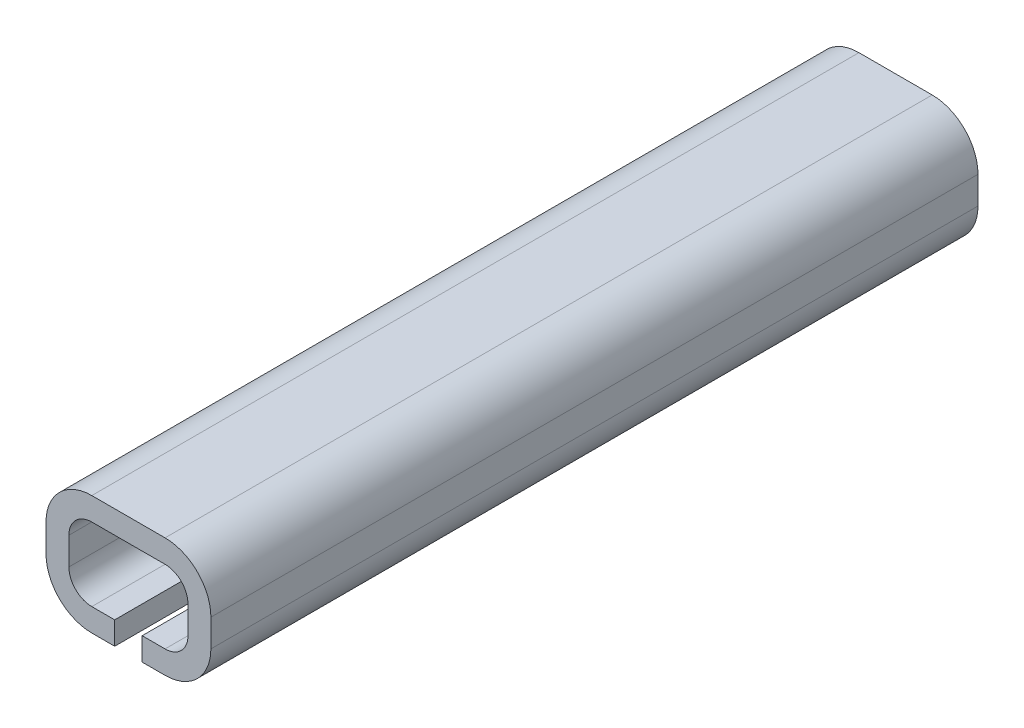
SolidWorks part; units mm, degrees
ref_plane "Plan de face" through (0, 0, 0) normal (0, 0, 1) x (1, 0, 0)
ref_plane "Plan de dessus" through (0, 0, 0) normal (0, 1, 0) x (1, 0, 0)
ref_plane "Plan de droite" through (0, 0, 0) normal (1, 0, 0) x (0, 0, -1)
sketch "Esquisse1" plane through (0, 0, 0) normal (0, 0, 1) x (1, 0, 0)
  line L1 (2.6, 0.6) -> (2.6, -0.6)
  line L2 (1.6, -1.6) -> (-1.6, -1.6)
  line L3 (-2.6, -0.6) -> (-2.6, 0.6)
  line L5 (3.6, 0.6) -> (3.6, -0.6)
  line L6 (1.6, -2.6) -> (-1.6, -2.6)
  line L7 (-3.6, -0.6) -> (-3.6, 0.6)
  line L16 (-1.6, 2.6) -> (1.6, 2.6) construction
  line L17 (1.6, 2.6) -> (0.1679, 2.6)
  line L18 (-1.6, 2.6) -> (0.1679, 2.6)
  line L19 (-1.6, 1.6) -> (1.6, 1.6)
  line L20 (-1.6, 1.6) -> (1.6, 1.6) construction
  arc A0 (-1.6, -1.6) -> (-2.6, -0.6) centre (-1.6, -0.6) cw
  arc A1 (2.6, -0.6) -> (1.6, -1.6) centre (1.6, -0.6) cw
  arc A2 (1.6, 1.6) -> (2.6, 0.6) centre (1.6, 0.6) cw
  arc A3 (-1.6, 1.6) -> (-2.6, 0.6) centre (-1.6, 0.6) ccw
  arc A4 (1.6, 2.6) -> (3.6, 0.6) centre (1.6, 0.6) cw
  arc A5 (3.6, -0.6) -> (1.6, -2.6) centre (1.6, -0.6) cw
  arc A6 (-1.6, -2.6) -> (-3.6, -0.6) centre (-1.6, -0.6) cw
  arc A7 (-1.6, 2.6) -> (-3.6, 0.6) centre (-1.6, 0.6) ccw
  point P6 (-2.6, -1.6)
  point P11 (5.1, 1.6)
  point P14 (-2.6, 1.6)
  point P15 (0, 1.6)
  point P16 (-2.6, 0)
  dimension "D3" = 1
  dimension "D1" = 3.2
  dimension "D2" = 5.2
  dimension "D9" = 3.2
  dimension "D4" = 1
extrude "Boss.-Extru.2" add sketch "Esquisse1" along normal blind 10
sketch "Esquisse7" plane through (0, 0, 0) normal (0, 0, -1) x (-1, 0, 0)
  line L8 (-3.6, 0.6) -> (-3.6, -0.6)
  line L9 (-1.6, -2.6) -> (1.6, -2.6)
  line L10 (3.6, -0.6) -> (3.6, 0.6)
  line L11 (1.6, 2.6) -> (-1.6, 2.6)
  line L16 (-3.6, 0.6) -> (-3.6, -0.6)
  line L17 (-1.6, -2.6) -> (1.6, -2.6)
  line L18 (3.6, -0.6) -> (3.6, 0.6)
  line L19 (1.6, 2.6) -> (-1.6, 2.6)
  arc A8 (-1.6, 2.6) -> (-3.6, 0.6) centre (-1.6, 0.6) ccw
  arc A9 (-3.6, -0.6) -> (-1.6, -2.6) centre (-1.6, -0.6) ccw
  arc A10 (1.6, -2.6) -> (3.6, -0.6) centre (1.6, -0.6) ccw
  arc A11 (3.6, 0.6) -> (1.6, 2.6) centre (1.6, 0.6) ccw
  arc A16 (-1.6, 2.6) -> (-3.6, 0.6) centre (-1.6, 0.6) ccw
  arc A17 (-3.6, -0.6) -> (-1.6, -2.6) centre (-1.6, -0.6) ccw
  arc A18 (1.6, -2.6) -> (3.6, -0.6) centre (1.6, -0.6) ccw
  arc A19 (3.6, 0.6) -> (1.6, 2.6) centre (1.6, 0.6) ccw
  dimension "D1" = 0
extrude "Boss.-Extru.4" add sketch "Esquisse7" along normal blind 6.75
mirror "Symétrie1" about plane through (1.6, 0.6, -6.75) normal (0, 0, -1) of "Boss.-Extru.4", "Boss.-Extru.2"
sketch "Esquisse5" plane through (0, -2.6, 0) normal (0, -1, 0) x (1, 0, 0)
  line L0 (1.6, -23.5) -> (-1.6, -23.5) construction
  line L1 (0.6, -23.5) -> (-0.6, -23.5)
  line L2 (0.6, -23.5) -> (0.6, -13.5)
  line L3 (0.6, -13.5) -> (-0.6, -13.5)
  line L4 (-0.6, -23.5) -> (-0.6, -13.5)
  line L5 (1.6, 10) -> (-1.6, 10) construction
  line L6 (-0.6, 10) -> (0.6, 10)
  line L7 (-0.6, 10) -> (-0.6, 0)
  line L8 (-0.6, 0) -> (0.6, 0)
  line L9 (0.6, 10) -> (0.6, 0)
  line L10 (-1.6, 10) -> (-1.6, -23.5) construction
  line L11 (1.6, 10) -> (1.6, -23.5) construction
  dimension "D1" = 10
  dimension "D2" = 10
  dimension "D3" = 1
  dimension "D4" = 1
extrude "Enlèv. mat.-Extru.1" cut sketch "Esquisse5" against normal up to surface (1 mm away) up to face at (0, -1.6, -18.5)
